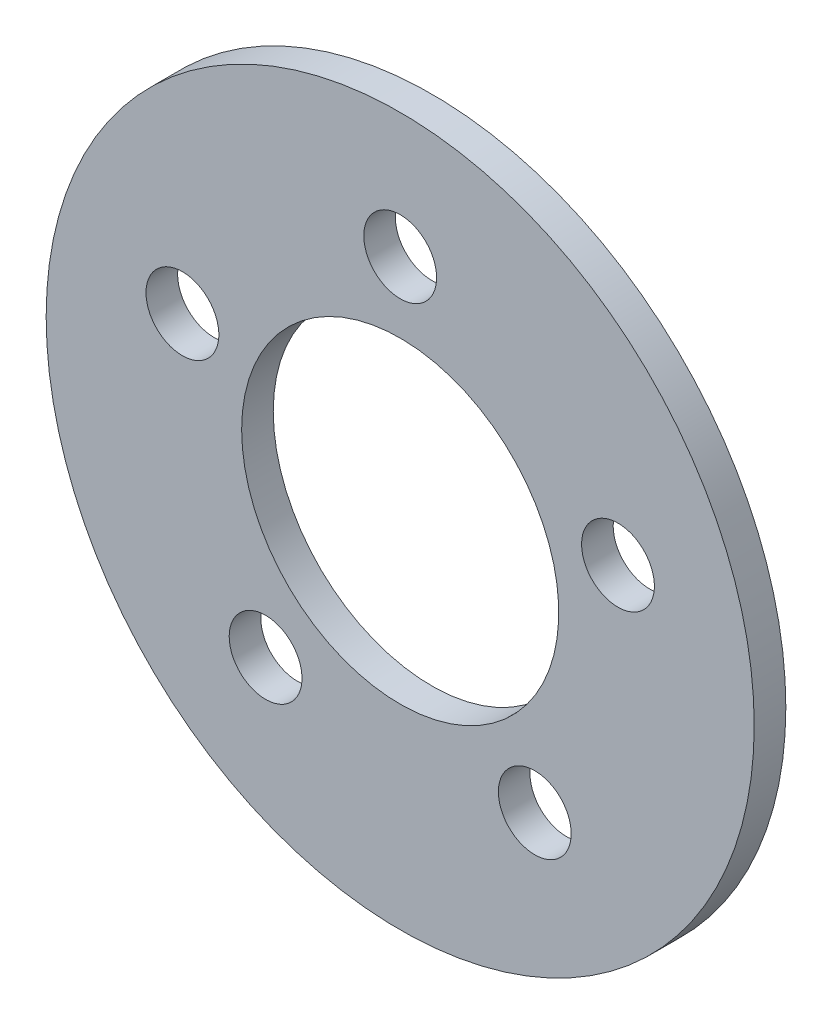
SolidWorks part; units mm, degrees
material "6061-T6 (SS)"
ref_plane "Front Plane" through (0, 0, 0) normal (0, 0, 1) x (1, 0, 0)
ref_plane "Top Plane" through (0, 0, 0) normal (0, 1, 0) x (1, 0, 0)
ref_plane "Right Plane" through (0, 0, 0) normal (1, 0, 0) x (0, 0, -1)
sketch "Sketch3" plane through (0, 0, -15.875) normal (0, 0, -1) x (-1, 0, 0)
  circle A0 centre (0, 0) radius 7.9629 construction
  circle A1 centre (0, 0) radius 7.9629
  circle A2 centre (0, 0) radius 17.78
  circle A3 centre (-6.7595, -9.3037) radius 1.8288 construction
  circle A4 centre (6.7595, -9.3037) radius 1.8288 construction
  circle A5 centre (10.9371, 3.5537) radius 1.8288 construction
  circle A6 centre (0, 11.5) radius 1.8288 construction
  circle A7 centre (-10.9371, 3.5537) radius 1.8288 construction
  circle A8 centre (-6.7595, -9.3037) radius 1.8288
  circle A9 centre (6.7595, -9.3037) radius 1.8288
  circle A10 centre (10.9371, 3.5537) radius 1.8288
  circle A11 centre (0, 11.5) radius 1.8288
  circle A12 centre (-10.9371, 3.5537) radius 1.8288
  dimension "D1" = 35.56
extrude "Boss-Extrude2" add sketch "Sketch3" along normal blind 1.5875
